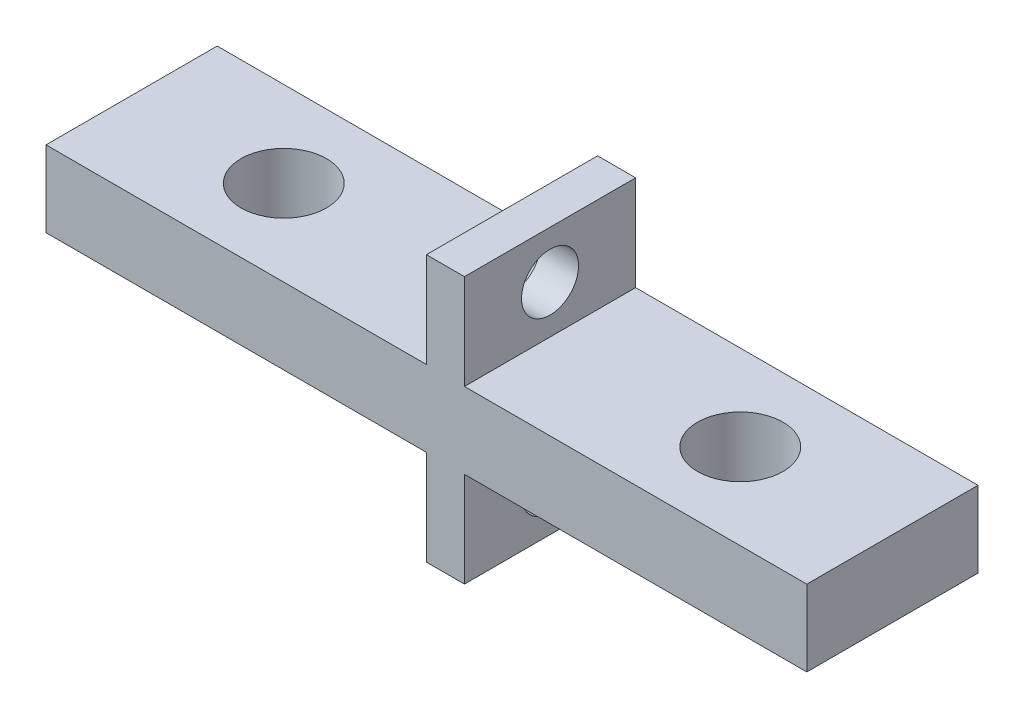
SolidWorks part; units mm, degrees
ref_plane "Front Plane" through (0, 0, 0) normal (0, 0, 1) x (1, 0, 0)
ref_plane "Top Plane" through (0, 0, 0) normal (0, 1, 0) x (1, 0, 0)
ref_plane "Right Plane" through (0, 0, 0) normal (1, 0, 0) x (0, 0, -1)
sketch "Sketch1" plane through (0, 0, 0) normal (0, 1, 0) x (1, 0, 0)
  line L1 (-7.2264, 5.3136) -> (32.7736, 5.3136)
  line L2 (-7.2264, 5.3136) -> (-7.2264, -3.6864)
  line L3 (-7.2264, -3.6864) -> (32.7736, -3.6864)
  line L4 (32.7736, 5.3136) -> (32.7736, -3.6864)
  dimension "D1" = 9
  dimension "D2" = 40
extrude "Boss-Extrude1" add sketch "Sketch1" along normal blind 4
hole_wizard "#8 Clearance Hole1" positions "3DSketch1" profile "Sketch2" hole size "#8" standard "ANSI Inch"
sketch3d "3DSketch1"
  line L0 (-7.2264, 4, -5.3136) -> (-7.2264, 4, 3.6864) construction
  line L1 (32.7736, 4, 3.6864) -> (32.7736, 4, -5.3136) construction
  line L2 (-7.2264, 4, 3.6864) -> (32.7736, 4, 3.6864) construction
  point P0 (0.7736, 4, -0.8136)
  point P2 (24.7736, 4, -0.8136)
  dimension "D1" = 8
  dimension "D2" = 8
  dimension "D3" = 4.5
  dimension "D4" = 4.5
  dimension "D5" = 24
sketch "Sketch2" plane through (0.7736, 4, -0.8136) normal (1, 0, 0) x (0, 0, 1)
  line L0 (0, 0) -> (0, 18.3507)
  line L1 (0, 18.3507) -> (2.2479, 17)
  line L2 (2.2479, 17) -> (2.2479, 0)
  line L5 (2.2479, 0) -> (0, 0)
  line L10 (0, 18.3507) -> (-2.2479, 17) construction
  line L11 (0, -6.35) -> (0, 107.95) construction
  dimension "Hole Dia." = 4.4958
  dimension "Hole Depth" = 17
  dimension "Drill Angle" = 118
sketch "Sketch5" plane through (0, 4, 0) normal (0, 1, 0) x (1, 0, 0)
  line L0 (-7.2264, -3.6864) -> (32.7736, -3.6864) construction
  line L1 (12.7736, -3.6864) -> (14.7736, -3.6864)
  line L2 (12.7736, -3.6864) -> (12.7736, 5.3136)
  line L3 (12.7736, 5.3136) -> (14.7736, 5.3136)
  line L4 (14.7736, -3.6864) -> (14.7736, 5.3136)
  line L5 (32.7736, 5.3136) -> (-7.2264, 5.3136) construction
  line L6 (-7.2264, 5.3136) -> (-7.2264, -3.6864) construction
  dimension "D1" = 20
  dimension "D2" = 18
extrude "Boss-Extrude2" add sketch "Sketch5" along normal blind 5 and the other way blind 9
sketch "Sketch6" plane through (12.7736, 0, 0) normal (-1, 0, 0) x (0, 0, 1)
  line L2 (-5.3136, 4) -> (-5.3136, 9) construction
  line L3 (-5.3136, -5) -> (-5.3136, 0) construction
  line L4 (-5.3136, 9) -> (3.6864, 9) construction
  line L5 (-5.3136, -5) -> (3.6864, -5) construction
  circle A0 centre (-0.8136, 6.5) radius 1.5
  circle A1 centre (-0.8136, -2.5) radius 1.5
  dimension "D1" = 4.5
  dimension "D5" = 3
  dimension "D6" = 3
  dimension "D2" = 4.5
  dimension "D3" = 2.5
  dimension "D4" = 2.5
extrude "Cut-Extrude1" cut sketch "Sketch6" against normal blind 2
